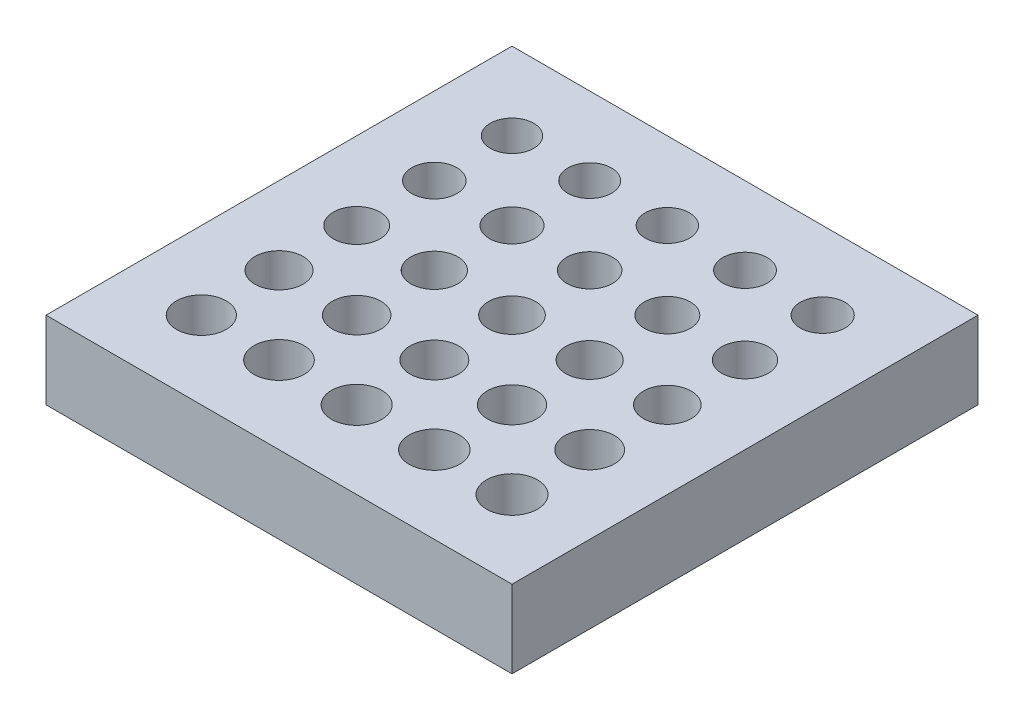
SolidWorks part; units mm, degrees
ref_plane "Front Plane" through (0, 0, 0) normal (0, 0, 1) x (1, 0, 0)
ref_plane "Top Plane" through (0, 0, 0) normal (0, 1, 0) x (1, 0, 0)
ref_plane "Right Plane" through (0, 0, 0) normal (1, 0, 0) x (0, 0, -1)
sketch "Sketch1" plane through (0, 0, 0) normal (0, 1, 0) x (1, 0, 0)
  line L1 (-19.05, -19.05) -> (19.05, -19.05)
  line L2 (-19.05, -19.05) -> (-19.05, 19.05)
  line L3 (-19.05, 19.05) -> (19.05, 19.05)
  line L4 (19.05, -19.05) -> (19.05, 19.05)
  line L5 (-19.05, -19.05) -> (19.05, 19.05) construction
  line L6 (-19.05, 19.05) -> (19.05, -19.05) construction
  circle A0 centre (-12.7, 12.7) radius 1.778
  circle A1 centre (-6.35, 12.7) radius 1.7907
  circle A2 centre (0, 12.7) radius 1.8034
  circle A3 centre (6.35, 12.7) radius 1.8161
  circle A4 centre (12.7, 12.7) radius 1.8288
  circle A5 centre (-6.35, 6.35) radius 1.8542
  circle A6 centre (0, 6.35) radius 1.8669
  circle A7 centre (6.35, 6.35) radius 1.8796
  circle A8 centre (12.7, 6.35) radius 1.8923
  circle A9 centre (-6.35, 0) radius 1.9177
  circle A10 centre (0, 0) radius 1.9304
  circle A11 centre (6.35, 0) radius 1.9431
  circle A12 centre (12.7, 0) radius 1.9558
  circle A13 centre (-6.35, -6.35) radius 1.9812
  circle A14 centre (0, -6.35) radius 1.9939
  circle A15 centre (6.35, -6.35) radius 2.0066
  circle A16 centre (12.7, -6.35) radius 2.0193
  circle A17 centre (-6.35, -12.7) radius 2.0447
  circle A18 centre (0, -12.7) radius 2.0574
  circle A19 centre (6.35, -12.7) radius 2.0701
  circle A20 centre (12.7, -12.7) radius 2.0828
  circle A21 centre (-12.7, 6.35) radius 1.8415
  circle A22 centre (-12.7, 0) radius 1.905
  circle A23 centre (-12.7, -6.35) radius 1.9685
  circle A24 centre (-12.7, -12.7) radius 2.032
  point P0 (0, 0)
  point P8 (0, 0)
  point P9 (-10.4046, 10.4046)
  point P10 (12.514, 12.514)
  point P59 (0, 0)
  dimension "D1" = 3.556
  dimension "D2" = 3.5814
  dimension "D5" = 3.6068
  dimension "D6" = 3.6322
  dimension "D7" = 3.6576
  dimension "D8" = 3.683
  dimension "D9" = 3.7084
  dimension "D10" = 3.7338
  dimension "D11" = 3.7592
  dimension "D12" = 3.7846
  dimension "D13" = 3.81
  dimension "D14" = 3.8354
  dimension "D15" = 3.8608
  dimension "D16" = 3.8862
  dimension "D17" = 3.9116
  dimension "D18" = 3.937
  dimension "D19" = 3.9624
  dimension "D20" = 3.9878
  dimension "D21" = 4.0132
  dimension "D22" = 4.0386
  dimension "D23" = 4.064
  dimension "D24" = 4.0894
  dimension "D25" = 4.1148
  dimension "D26" = 4.1402
  dimension "D27" = 4.1656
  dimension "D3" = 38.1
  dimension "D4" = 6.35
extrude "Boss-Extrude1" add sketch "Sketch1" along normal blind 6.35
